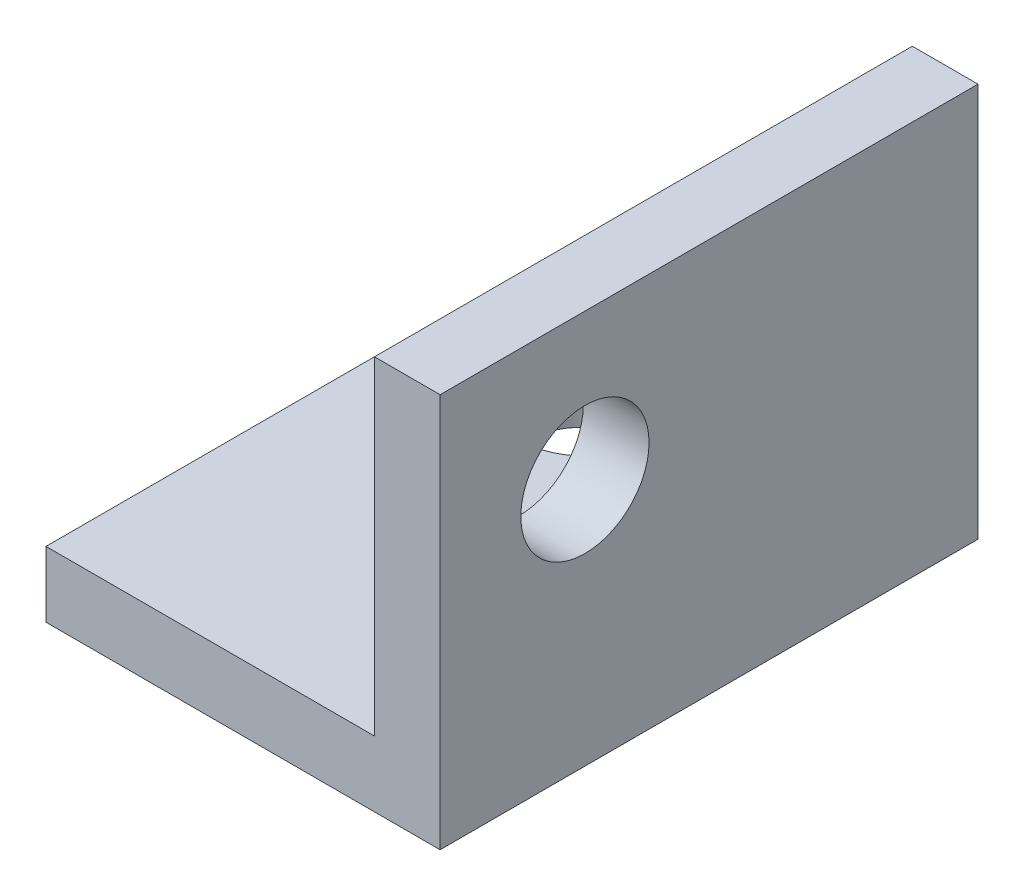
SolidWorks part; units mm, degrees
ref_plane "Front Plane" through (0, 0, 0) normal (0, 0, 1) x (1, 0, 0)
ref_plane "Top Plane" through (0, 0, 0) normal (0, 1, 0) x (1, 0, 0)
ref_plane "Right Plane" through (0, 0, 0) normal (1, 0, 0) x (0, 0, -1)
sketch "Sketch1" plane through (0, 0, 0) normal (0, 0, 1) x (1, 0, 0)
  line L0 (-4.7625, -4.7625) -> (4.7625, -4.7625) construction
  line L1 (4.7625, -4.7625) -> (4.7625, 4.7625) construction
  line L2 (4.7625, 4.7625) -> (3.175, 4.7625) construction
  line L3 (3.175, 4.7625) -> (3.175, -3.175) construction
  line L4 (3.175, -3.175) -> (-4.7625, -3.175) construction
  line L5 (-4.7625, -4.7625) -> (-4.7625, -3.175) construction
  line L6 (3.9688, 4.7625) -> (4.7625, 4.7625) construction
  line L7 (-4.7625, -3.9688) -> (-4.7625, -4.7625) construction
  line L8 (0, 0) -> (4.7625, 0) construction
  line L9 (0, 0) -> (0, -4.7625) construction
  point P3 (0, -4.7625)
  point P5 (3.175, -4.7625)
  point P8 (-4.7625, -4.7625)
  point P12 (-4.7625, -3.175)
  point P17 (3.175, 4.7625)
  dimension "Outside Height" = 9.525
  dimension "Outside Width" = 9.525
  dimension "Wall Thickness" = 1.5875
  dimension "Inside Width" = 7.9375
  dimension "Inside Height" = 7.9375
sketch "Sketch2" [suppressed] plane through (0, 0, 0) normal (1, 0, 0) x (0, 0, -1)
  line L0 (0, 0) -> (609.6, 0) construction
  line L1 (0, 0) -> (-609.6, 0) construction
  line L2 (0, -4.7625) -> (609.6, -4.7625) construction
  line L3 (609.6, -4.7625) -> (609.6, 0) construction
  line L4 (0, -4.7625) -> (-609.6, -4.7625) construction
  line L5 (-609.6, -4.7625) -> (-609.6, 0) construction
  point P3 (600.075, 0)
  point P5 (609.6, 0)
  point P6 (-600.075, 0)
  point P7 (-609.6, 0)
  dimension "D1" = 9.525
  dimension "D2" = 9.525
  dimension "Length" = 1219.2
sketch "Sketch3" plane through (0, 0, 0) normal (0, 0, 1) x (1, 0, 0)
  line L0 (3.175, -3.175) -> (-4.7625, -3.175) construction
  line L1 (-4.7625, -4.7625) -> (-4.7625, -3.175) construction
  line L2 (-4.7625, -4.7625) -> (4.7625, -4.7625) construction
  line L3 (4.7625, -4.7625) -> (4.7625, 4.7625) construction
  line L4 (4.7625, 4.7625) -> (3.175, 4.7625) construction
  line L5 (3.175, 4.7625) -> (3.175, -3.175) construction
  line L6 (3.175, -3.175) -> (-4.7625, -3.175)
  line L7 (-4.7625, -4.7625) -> (-4.7625, -3.175)
  line L8 (-4.7625, -4.7625) -> (4.7625, -4.7625)
  line L9 (4.7625, -4.7625) -> (4.7625, 4.7625)
  line L10 (4.7625, 4.7625) -> (3.175, 4.7625)
  line L11 (3.175, 4.7625) -> (3.175, -3.175)
extrude "Boss-Extrude1" add sketch "Sketch3" along normal mid plane 13
sketch "Sketch4" plane through (4.7625, 0, 0) normal (1, 0, 0) x (0, 0, -1)
  line L0 (-6.5, -4.7625) -> (6.5, -4.7625) construction
  line L2 (-6.5, -4.7625) -> (-6.5, 4.7625) construction
  circle A0 centre (-3, 1.2375) radius 1.55
  dimension "D1" = 3.1
  dimension "D2" = 6
  dimension "D3" = 3.5
extrude "Cut-Extrude1" cut sketch "Sketch4" against normal blind 10
sketch "Sketch5" plane through (0, -4.7625, 0) normal (0, -1, 0) x (1, 0, 0)
  line L0 (4.7625, 6.5) -> (4.7625, -6.5) construction
  line L1 (-4.7625, -6.5) -> (4.7625, -6.5) construction
  circle A0 centre (-1.2375, -3) radius 1.55
  dimension "D1" = 3.1
  dimension "D2" = 6
  dimension "D3" = 3.5
extrude "Cut-Extrude2" cut sketch "Sketch5" against normal blind 10
equation "\"D2@Sketch2\"=\"D1@Sketch2\""
equation "\"D1@Sketch2\"=\"outside height@sketch1\""
